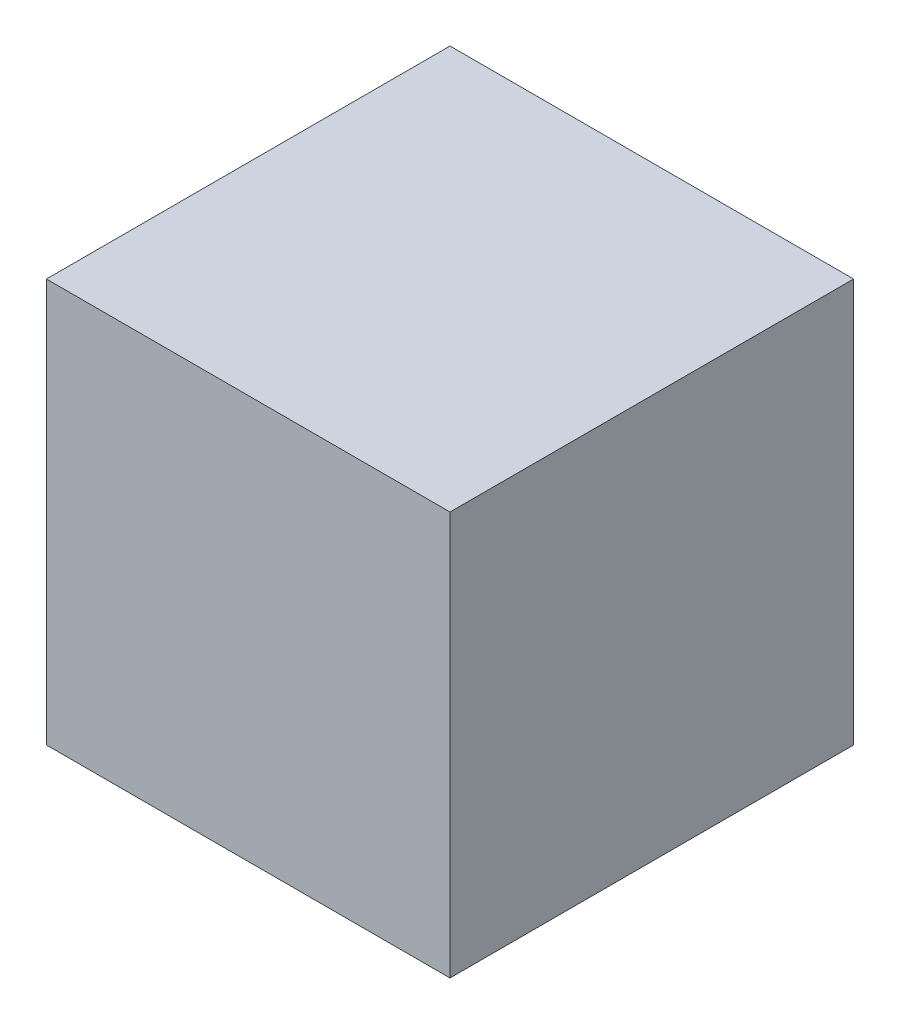
SolidWorks part; units mm, degrees
material "PVC 0.007 Plasticized"
ref_plane "Front Plane" through (0, 0, 0) normal (0, 0, 1) x (1, 0, 0)
ref_plane "Top Plane" through (0, 0, 0) normal (0, 1, 0) x (1, 0, 0)
ref_plane "Right Plane" through (0, 0, 0) normal (1, 0, 0) x (0, 0, -1)
sketch "Sketch1" plane through (0, 0, 0) normal (0, 0, 1) x (1, 0, 0)
  line L1 (-28.5, -28.5) -> (28.5, -28.5)
  line L2 (-28.5, -28.5) -> (-28.5, 28.5)
  line L3 (-28.5, 28.5) -> (28.5, 28.5)
  line L4 (28.5, -28.5) -> (28.5, 28.5)
  line L5 (-28.5, -28.5) -> (28.5, 28.5) construction
  line L6 (-28.5, 28.5) -> (28.5, -28.5) construction
  point P0 (0, 0)
  dimension "D1" = 57
  dimension "D2" = 57
extrude "Boss-Extrude1" add sketch "Sketch1" along normal blind 57
